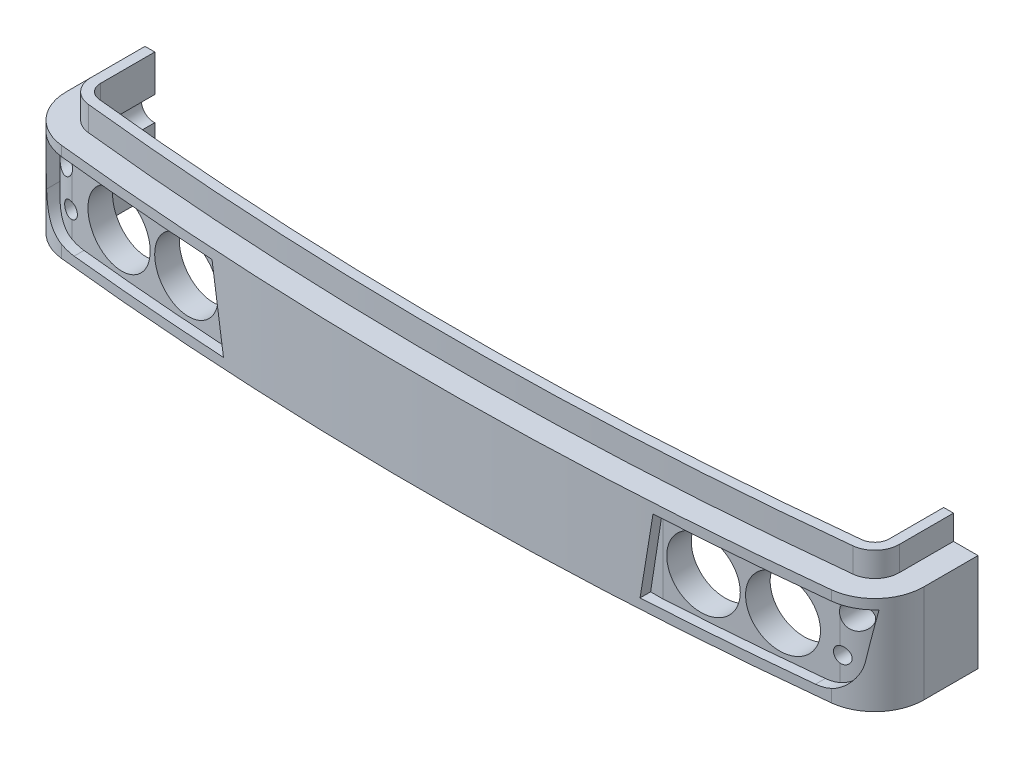
SolidWorks part; units mm, degrees
ref_plane "Front Plane" through (0, 0, 0) normal (0, 0, 1) x (1, 0, 0)
ref_plane "Top Plane" through (0, 0, 0) normal (0, 1, 0) x (1, 0, 0)
ref_plane "Right Plane" through (0, 0, 0) normal (1, 0, 0) x (0, 0, -1)
sketch "Sketch1" plane through (0, 0, 0) normal (0, 1, 0) x (1, 0, 0)
  line L1 (-87.5, 10) -> (87.5, 10)
  line L2 (-87.5, 10) -> (-87.5, -1.0675)
  line L3 (-87.5, -10) -> (87.5, -10) construction
  line L4 (87.5, 10) -> (87.5, -1.0675)
  line L5 (-87.5, 10) -> (87.5, -10) construction
  line L6 (-87.5, -10) -> (87.5, 10) construction
  arc A0 (-78.5634, -11.0108) -> (78.5634, -11.0108) centre (0, 723.5779) ccw
  arc A1 (78.5634, -11.0108) -> (87.5, -1.0675) centre (77.5, -1.0675) ccw
  arc A2 (-78.5634, -11.0108) -> (-87.5, -1.0675) centre (-77.5, -1.0675) cw
  point P0 (0, 0)
  point P7 (0, -15.2)
  point P8 (0, -10)
  dimension "D4" = 10
  dimension "D1" = 175
  dimension "D2" = 20
  dimension "D3" = 5.2
extrude "Boss-Extrude1" add sketch "Sketch1" along normal blind 20
ref_plane "Plane1" through (0, 0, 18) normal (0, 0, 1) x (1, 0, 0)
sketch "Sketch2" plane through (0, 0, 18) normal (0, 0, 1) x (1, 0, 0)
  line L0 (0, 28.9371) -> (0, 0) construction
  line L1 (-85, 18) -> (-45, 18)
  line L3 (-75.6529, 2) -> (-45.0081, 2)
  line L5 (78.5634, 20) -> (-78.5634, 20) construction
  line L7 (-85, 18) -> (-83.557, 8.765)
  line L8 (-87.5, 20) -> (-87.5, 0) construction
  line L9 (-45, 18) -> (-42.5081, 2)
  line L10 (-42.5081, 2) -> (-45.0081, 2)
  line L11 (45, 18) -> (42.5081, 2)
  line L12 (85, 18) -> (45, 18)
  line L13 (85, 18) -> (83.557, 8.765)
  line L14 (75.6529, 2) -> (45.0081, 2)
  line L15 (42.5081, 2) -> (45.0081, 2)
  arc A0 (-75.6529, 2) -> (-83.557, 8.765) centre (-75.6529, 10) cw
  arc A1 (75.6529, 2) -> (83.557, 8.765) centre (75.6529, 10) ccw
  point P13 (-82.5, 2)
  dimension "D6" = 8
  dimension "D1" = 40
  dimension "D2" = 16
  dimension "D3" = 2
  dimension "D4" = 2.5
  dimension "D5" = 5
  dimension "D7" = 2.5
extrude "Cut-Extrude3" cut sketch "Sketch2" against normal through all both and the other way through all
sketch "Sketch7" plane through (0, 18, 0) normal (0, -1, 0) x (1, 0, 0)
  line L0 (-85, -10) -> (-85, 7.6819) construction
  line L1 (-85, -10) -> (-85, 3.8514)
  line L2 (-45, -10) -> (-45, 13.8282) construction
  line L3 (-45, -10) -> (-45, 11.8245)
  line L4 (-45, -10) -> (-85, -10) construction
  line L5 (-45, -10) -> (-85, -10)
  arc A10 (-78.3507, 9.0222) -> (-85.5, 1.0675) centre (-77.5, 1.0675) ccw
  arc A11 (78.3507, 9.0222) -> (-78.3507, 9.0222) centre (0, -723.5779) ccw
  arc A12 (-78.3507, 9.0222) -> (-85, 3.8514) centre (-77.5, 1.0675) ccw
  arc A13 (-45, 11.8245) -> (-78.3507, 9.0222) centre (0, -723.5779) ccw
  dimension "D1" = 2
extrude "Boss-Extrude5" add sketch "Sketch7" along normal up to surface (16 mm away) up to face at (-59.0842, 2, 1.3697)
sketch "Sketch8" plane through (-45, 0, 0) normal (1, 0, 0) x (0, 0, -1)
  line L4 (-11.8245, 2) -> (10, 2)
  line L5 (10, 2) -> (10, 18)
  line L6 (10, 18) -> (-11.8245, 18)
  line L7 (-11.8245, 18) -> (-11.8245, 2)
  line L8 (-11.8245, 2) -> (10, 2)
  line L9 (10, 2) -> (10, 18)
  line L10 (10, 18) -> (-11.8245, 18)
  line L11 (-11.8245, 18) -> (-11.8245, 2)
  dimension "D1" = 0
extrude "Boss-Extrude6" add sketch "Sketch8" along normal blind 11.5
mirror "Mirror1" about plane through (0, 0, 0) normal (1, 0, 0) of "Boss-Extrude6", "Boss-Extrude5"
sketch "Sketch9" plane through (0, 20, 0) normal (0, 1, 0) x (1, 0, 0)
  line L9 (-80.5, 10) -> (-80.5, -1.0675)
  line L10 (80.5, -1.0675) -> (80.5, 10)
  line L11 (82.5, -1.0675) -> (82.5, 10)
  line L12 (-82.5, 10) -> (-82.5, -1.0675)
  line L13 (82.5, -1.0675) -> (82.5, 10)
  line L14 (-82.5, 10) -> (-82.5, -1.0675)
  line L15 (-82.5, 10) -> (-80.5, 10)
  line L16 (82.5, 10) -> (80.5, 10)
  arc A12 (-80.5, -1.0675) -> (-77.819, -4.0505) centre (-77.5, -1.0675) ccw
  arc A13 (-77.819, -4.0505) -> (77.819, -4.0505) centre (0, 723.5779) ccw
  arc A14 (77.819, -4.0505) -> (80.5, -1.0675) centre (77.5, -1.0675) ccw
  arc A15 (78.0317, -6.0392) -> (82.5, -1.0675) centre (77.5, -1.0675) ccw
  arc A16 (-78.0317, -6.0392) -> (78.0317, -6.0392) centre (0, 723.5779) ccw
  arc A17 (-82.5, -1.0675) -> (-78.0317, -6.0392) centre (-77.5, -1.0675) ccw
  arc A18 (78.0317, -6.0392) -> (82.5, -1.0675) centre (77.5, -1.0675) ccw
  arc A19 (-78.0317, -6.0392) -> (78.0317, -6.0392) centre (0, 723.5779) ccw
  arc A20 (-82.5, -1.0675) -> (-78.0317, -6.0392) centre (-77.5, -1.0675) ccw
  dimension "D1" = 5
  dimension "D2" = 2
extrude "Boss-Extrude7" add sketch "Sketch9" along normal blind 5
sketch "Sketch10" plane through (0, 20, 0) normal (0, 1, 0) x (1, 0, 0)
  line L3 (-80.5, 10) -> (-80.5, -1.0675)
  line L4 (80.5, -1.0675) -> (80.5, 10)
  line L5 (80.5, 10) -> (-80.5, 10)
  line L6 (-80.5, 10) -> (-80.5, -1.0675)
  line L7 (80.5, -1.0675) -> (80.5, 10)
  line L8 (80.5, 10) -> (-80.5, 10)
  arc A3 (-80.5, -1.0675) -> (-77.819, -4.0505) centre (-77.5, -1.0675) ccw
  arc A4 (-77.819, -4.0505) -> (77.819, -4.0505) centre (0, 723.5779) ccw
  arc A5 (77.819, -4.0505) -> (80.5, -1.0675) centre (77.5, -1.0675) ccw
  arc A6 (-80.5, -1.0675) -> (-77.819, -4.0505) centre (-77.5, -1.0675) ccw
  arc A7 (-77.819, -4.0505) -> (77.819, -4.0505) centre (0, 723.5779) ccw
  arc A8 (77.819, -4.0505) -> (80.5, -1.0675) centre (77.5, -1.0675) ccw
  dimension "D1" = 0
extrude "Cut-Extrude6" cut sketch "Sketch10" against normal through all
sketch "Sketch11" plane through (0, 0, 18) normal (0, 0, 1) x (1, 0, 0)
  line L0 (0, 25) -> (0, 0) construction
  line L1 (78.0317, 25) -> (-78.0317, 25) construction
  line L2 (-43.754, 10) -> (-83.75, 10) construction
  line L3 (-42.5081, 2) -> (-45, 18) construction
  line L4 (-83.557, 8.765) -> (-85, 18) construction
  line L5 (-85, 18) -> (-78.5634, 18) construction
  circle A1 centre (-52.754, 10) radius 7
  circle A2 centre (-67.754, 10) radius 7
  circle A3 centre (-80.754, 15) radius 2.5
  circle A4 centre (-78.754, 7.5) radius 1.6
  circle A5 centre (80.754, 15) radius 2.5
  circle A6 centre (78.754, 7.5) radius 1.6
  circle A7 centre (52.754, 10) radius 7
  circle A8 centre (67.754, 10) radius 7
  dimension "D1" = 14
  dimension "D2" = 14
  dimension "D5" = 5
  dimension "D8" = 3.2
  dimension "D3" = 15
  dimension "D4" = 9
  dimension "D6" = 3
  dimension "D7" = 13
  dimension "D9" = 11
  dimension "D10" = 2.5
extrude "Cut-Extrude7" cut sketch "Sketch11" against normal through all
